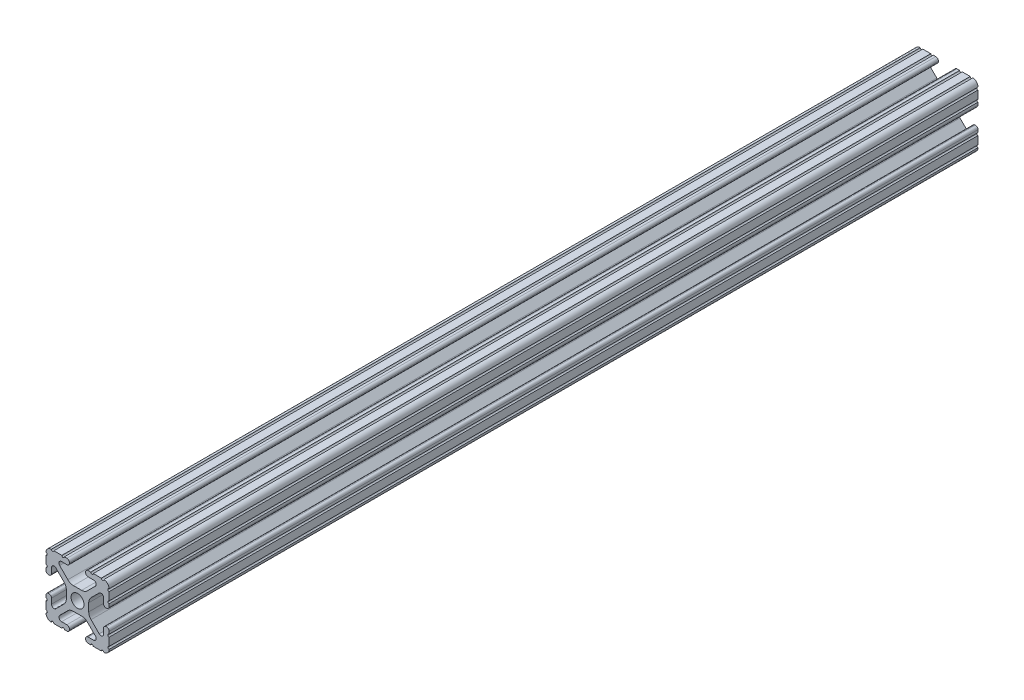
SolidWorks part; units mm, degrees
material "1060 Alloy"
ref_plane "Front Plane" through (0, 0, 0) normal (0, 0, 1) x (1, 0, 0)
ref_plane "Top Plane" through (0, 0, 0) normal (0, 1, 0) x (1, 0, 0)
ref_plane "Right Plane" through (0, 0, 0) normal (1, 0, 0) x (0, 0, -1)
sketch "Sketch1" plane through (0, 0, 0) normal (0, 0, 1) x (1, 0, 0)
  line L88 (-7.1797, -8.6452) -> (-3.9523, -5.4237)
  line L89 (-1.7093, -4.4958) -> (1.7093, -4.4958)
  line L90 (3.9523, -5.4237) -> (7.1797, -8.6452)
  line L91 (6.4164, -10.4902) -> (4.2875, -10.4902)
  line L92 (3.2385, -11.5392) -> (3.2385, -11.651)
  line L93 (4.2875, -12.7) -> (5.3171, -12.7)
  line L94 (6.3331, -12.7) -> (9.5504, -12.7)
  line L95 (12.7, -9.5504) -> (12.7, -6.3331)
  line L96 (12.7, -5.3171) -> (12.7, -4.2875)
  line L97 (11.651, -3.2385) -> (11.5392, -3.2385)
  line L98 (10.4902, -4.2875) -> (10.4902, -6.4021)
  line L99 (8.7371, -7.1294) -> (5.441, -3.8408)
  line L100 (4.5085, -1.5932) -> (4.5085, 1.5932)
  line L101 (5.441, 3.8408) -> (8.7371, 7.1294)
  line L102 (10.4902, 6.4021) -> (10.4902, 4.2875)
  line L103 (11.5392, 3.2385) -> (11.651, 3.2385)
  line L104 (12.7, 4.2875) -> (12.7, 5.3171)
  line L105 (12.7, 6.3331) -> (12.7, 9.5504)
  line L106 (9.5504, 12.7) -> (6.3331, 12.7)
  line L107 (5.3171, 12.7) -> (4.2875, 12.7)
  line L108 (3.2385, 11.651) -> (3.2385, 11.5392)
  line L109 (4.2875, 10.4902) -> (6.4768, 10.4902)
  line L110 (7.207, 8.7244) -> (3.8983, 5.4232)
  line L111 (1.6558, 4.4958) -> (-1.6558, 4.4958)
  line L112 (-3.8983, 5.4232) -> (-7.207, 8.7244)
  line L113 (-6.4768, 10.4902) -> (-4.2875, 10.4902)
  line L114 (-3.2385, 11.5392) -> (-3.2385, 11.651)
  line L115 (-4.2875, 12.7) -> (-5.3171, 12.7)
  line L116 (-6.3331, 12.7) -> (-9.5504, 12.7)
  line L117 (-12.7, 9.5504) -> (-12.7, 6.3331)
  line L118 (-12.7, 5.3171) -> (-12.7, 4.2875)
  line L119 (-11.651, 3.2385) -> (-11.5392, 3.2385)
  line L120 (-10.4902, 4.2875) -> (-10.4902, 6.4021)
  line L121 (-8.7371, 7.1294) -> (-5.441, 3.8408)
  line L122 (-4.5085, 1.5932) -> (-4.5085, -1.5932)
  line L123 (-5.441, -3.8408) -> (-8.7371, -7.1294)
  line L124 (-10.4902, -6.4021) -> (-10.4902, -4.2875)
  line L125 (-11.5392, -3.2385) -> (-11.651, -3.2385)
  line L126 (-12.7, -4.2875) -> (-12.7, -5.3171)
  line L127 (-12.7, -6.3331) -> (-12.7, -9.5504)
  line L128 (-9.5504, -12.7) -> (-6.3331, -12.7)
  line L129 (-5.3171, -12.7) -> (-4.2875, -12.7)
  line L130 (-3.2385, -11.651) -> (-3.2385, -11.5392)
  line L131 (-4.2875, -10.4902) -> (-6.4164, -10.4902)
  circle A1 centre (0, 0) radius 2.6035
  arc A104 (-7.1797, -8.6452) -> (-6.4164, -10.4902) centre (-6.4164, -9.4098) ccw
  arc A105 (-1.7093, -4.4958) -> (-3.9523, -5.4237) centre (-1.7093, -7.6708) ccw
  arc A106 (3.9523, -5.4237) -> (1.7093, -4.4958) centre (1.7093, -7.6708) ccw
  arc A107 (6.4164, -10.4902) -> (7.1797, -8.6452) centre (6.4164, -9.4098) ccw
  arc A108 (4.2875, -10.4902) -> (3.2385, -11.5392) centre (4.2875, -11.5392) ccw
  arc A109 (3.2385, -11.651) -> (4.2875, -12.7) centre (4.2875, -11.651) ccw
  arc A110 (6.3331, -12.7) -> (5.3171, -12.7) centre (5.8251, -12.7) ccw
  arc A111 (10.5664, -12.6998) -> (9.5504, -12.7) centre (10.0584, -12.7) ccw
  arc A112 (10.5664, -12.6998) -> (12.6998, -10.5664) centre (10.5918, -10.5918) ccw
  arc A113 (12.7, -9.5504) -> (12.6998, -10.5664) centre (12.7, -10.0584) ccw
  arc A114 (12.7, -5.3171) -> (12.7, -6.3331) centre (12.7, -5.8251) ccw
  arc A115 (12.7, -4.2875) -> (11.651, -3.2385) centre (11.651, -4.2875) ccw
  arc A116 (11.5392, -3.2385) -> (10.4902, -4.2875) centre (11.5392, -4.2875) ccw
  arc A117 (8.7371, -7.1294) -> (10.4902, -6.4021) centre (9.4628, -6.4021) ccw
  arc A118 (4.5085, -1.5932) -> (5.441, -3.8408) centre (7.6835, -1.5932) ccw
  arc A119 (5.441, 3.8408) -> (4.5085, 1.5932) centre (7.6835, 1.5932) ccw
  arc A120 (10.4902, 6.4021) -> (8.7371, 7.1294) centre (9.4628, 6.4021) ccw
  arc A121 (10.4902, 4.2875) -> (11.5392, 3.2385) centre (11.5392, 4.2875) ccw
  arc A122 (11.651, 3.2385) -> (12.7, 4.2875) centre (11.651, 4.2875) ccw
  arc A123 (12.7, 6.3331) -> (12.7, 5.3171) centre (12.7, 5.8251) ccw
  arc A124 (12.6998, 10.5664) -> (12.7, 9.5504) centre (12.7, 10.0584) ccw
  arc A125 (12.6998, 10.5664) -> (10.5664, 12.6998) centre (10.5918, 10.5918) ccw
  arc A126 (9.5504, 12.7) -> (10.5664, 12.6998) centre (10.0584, 12.7) ccw
  arc A127 (5.3171, 12.7) -> (6.3331, 12.7) centre (5.8251, 12.7) ccw
  arc A128 (4.2875, 12.7) -> (3.2385, 11.651) centre (4.2875, 11.651) ccw
  arc A129 (3.2385, 11.5392) -> (4.2875, 10.4902) centre (4.2875, 11.5392) ccw
  arc A130 (7.207, 8.7244) -> (6.4768, 10.4902) centre (6.4768, 9.4563) ccw
  arc A131 (1.6558, 4.4958) -> (3.8983, 5.4232) centre (1.6558, 7.6708) ccw
  arc A132 (-3.8983, 5.4232) -> (-1.6558, 4.4958) centre (-1.6558, 7.6708) ccw
  arc A133 (-6.4768, 10.4902) -> (-7.207, 8.7244) centre (-6.4768, 9.4563) ccw
  arc A134 (-4.2875, 10.4902) -> (-3.2385, 11.5392) centre (-4.2875, 11.5392) ccw
  arc A135 (-3.2385, 11.651) -> (-4.2875, 12.7) centre (-4.2875, 11.651) ccw
  arc A136 (-6.3331, 12.7) -> (-5.3171, 12.7) centre (-5.8251, 12.7) ccw
  arc A137 (-10.5664, 12.6998) -> (-9.5504, 12.7) centre (-10.0584, 12.7) ccw
  arc A138 (-10.5664, 12.6998) -> (-12.6998, 10.5664) centre (-10.5918, 10.5918) ccw
  arc A139 (-12.7, 9.5504) -> (-12.6998, 10.5664) centre (-12.7, 10.0584) ccw
  arc A140 (-12.7, 5.3171) -> (-12.7, 6.3331) centre (-12.7, 5.8251) ccw
  arc A141 (-12.7, 4.2875) -> (-11.651, 3.2385) centre (-11.651, 4.2875) ccw
  arc A142 (-11.5392, 3.2385) -> (-10.4902, 4.2875) centre (-11.5392, 4.2875) ccw
  arc A143 (-8.7371, 7.1294) -> (-10.4902, 6.4021) centre (-9.4628, 6.4021) ccw
  arc A144 (-4.5085, 1.5932) -> (-5.441, 3.8408) centre (-7.6835, 1.5932) ccw
  arc A145 (-5.441, -3.8408) -> (-4.5085, -1.5932) centre (-7.6835, -1.5932) ccw
  arc A146 (-10.4902, -6.4021) -> (-8.7371, -7.1294) centre (-9.4628, -6.4021) ccw
  arc A147 (-10.4902, -4.2875) -> (-11.5392, -3.2385) centre (-11.5392, -4.2875) ccw
  arc A148 (-11.651, -3.2385) -> (-12.7, -4.2875) centre (-11.651, -4.2875) ccw
  arc A149 (-12.7, -6.3331) -> (-12.7, -5.3171) centre (-12.7, -5.8251) ccw
  arc A150 (-12.6998, -10.5664) -> (-12.7, -9.5504) centre (-12.7, -10.0584) ccw
  arc A151 (-12.6998, -10.5664) -> (-10.5664, -12.6998) centre (-10.5918, -10.5918) ccw
  arc A152 (-9.5504, -12.7) -> (-10.5664, -12.6998) centre (-10.0584, -12.7) ccw
  arc A153 (-5.3171, -12.7) -> (-6.3331, -12.7) centre (-5.8251, -12.7) ccw
  arc A154 (-4.2875, -12.7) -> (-3.2385, -11.651) centre (-4.2875, -11.651) ccw
  arc A155 (-3.2385, -11.5392) -> (-4.2875, -10.4902) centre (-4.2875, -11.5392) ccw
extrude "Boss-Extrude1" add sketch "Sketch1" along normal blind 350
